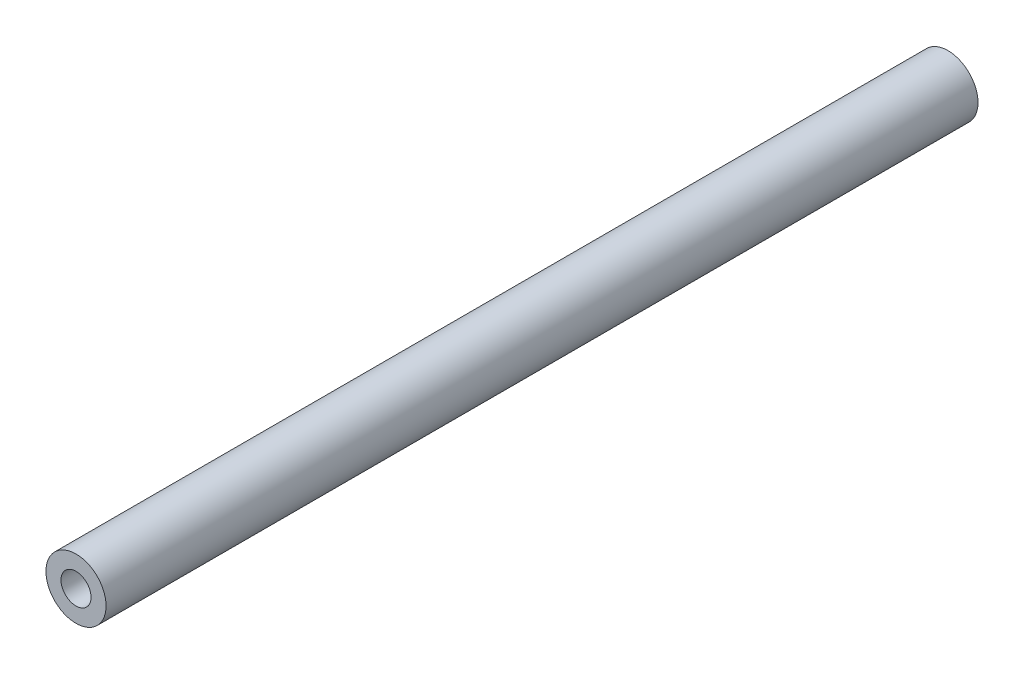
SolidWorks part; units mm, degrees
ref_plane "Front Plane" through (0, 0, 0) normal (0, 0, 1) x (1, 0, 0)
ref_plane "Top Plane" through (0, 0, 0) normal (0, 1, 0) x (1, 0, 0)
ref_plane "Right Plane" through (0, 0, 0) normal (1, 0, 0) x (0, 0, -1)
sketch "Sketch1" plane through (0, 0, 0) normal (0, 0, 1) x (1, 0, 0)
  circle A0 centre (0, 0) radius 10
  circle A1 centre (0, 0) radius 5
  dimension "D1" = 20
  dimension "D2" = 10
extrude "Boss-Extrude1" add sketch "Sketch1" along normal blind 290
